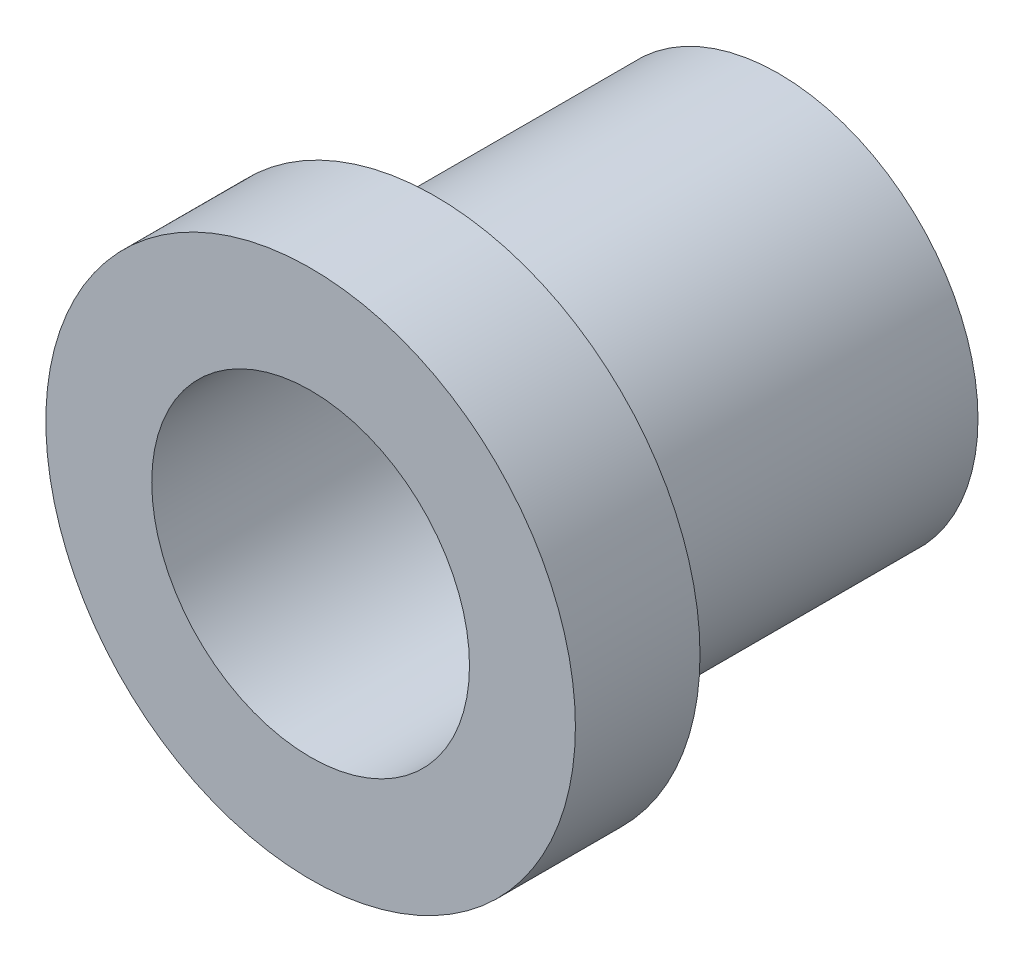
SolidWorks part; units mm, degrees
ref_plane "Front Plane" through (0, 0, 0) normal (0, 0, 1) x (1, 0, 0)
ref_plane "Top Plane" through (0, 0, 0) normal (0, 1, 0) x (1, 0, 0)
ref_plane "Right Plane" through (0, 0, 0) normal (1, 0, 0) x (0, 0, -1)
sketch "Sketch1" plane through (0, 0, 0) normal (0, 0, 1) x (1, 0, 0)
  circle A0 centre (0, 0) radius 5.3975
  circle A1 centre (0, 0) radius 3.2385
  dimension "D1" = 10.795
  dimension "D2" = 6.477
extrude "Boss-Extrude1" add sketch "Sketch1" along normal blind 2.54
sketch "Sketch2" plane through (0, 0, 0) normal (0, 0, -1) x (-1, 0, 0)
  circle A0 centre (0, 0) radius 3.2385
  circle A1 centre (0, 0) radius 4.064
  dimension "D1" = 6.477
  dimension "D2" = 8.128
extrude "Boss-Extrude2" add sketch "Sketch2" along normal blind 7
